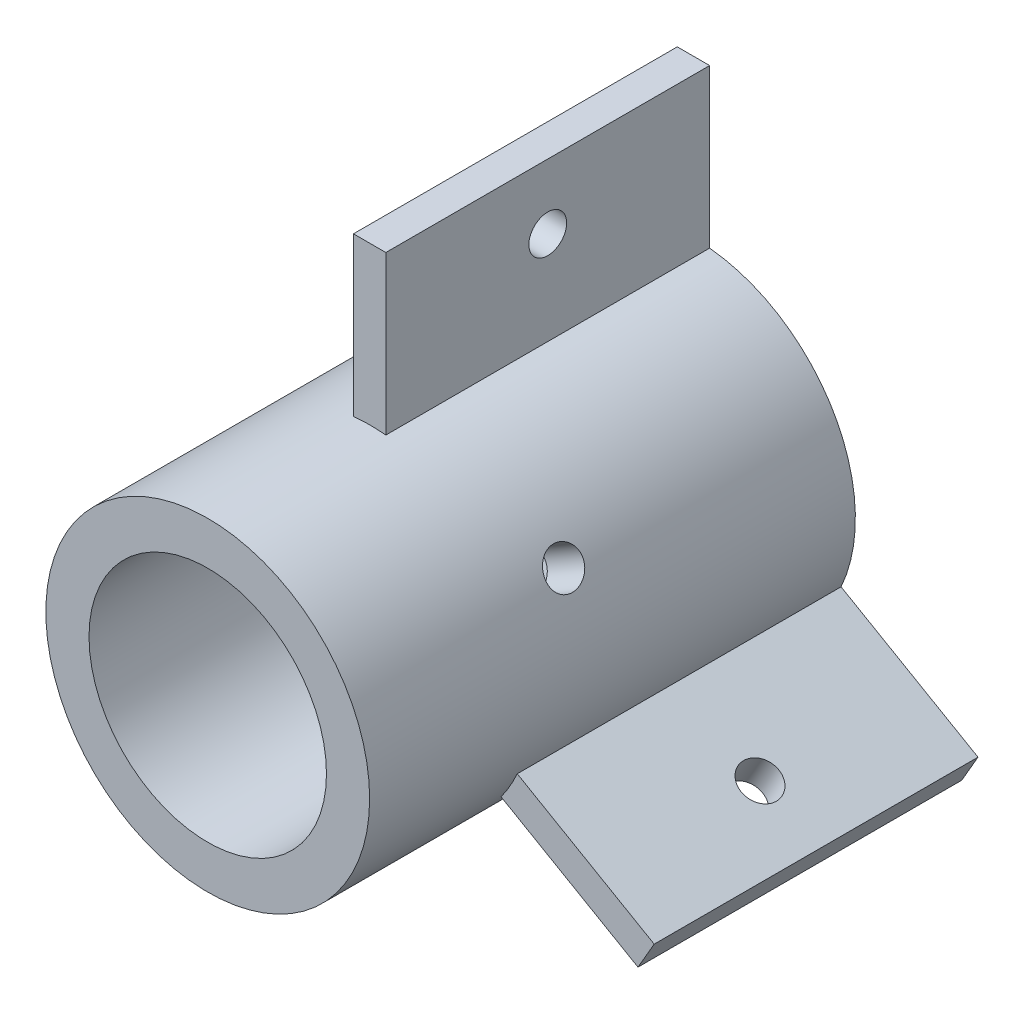
SolidWorks part; units mm, degrees
ref_plane "前基準面" through (0, 0, 0) normal (0, 0, 1) x (1, 0, 0)
ref_plane "上基準面" through (0, 0, 0) normal (0, 1, 0) x (1, 0, 0)
ref_plane "右基準面" through (0, 0, 0) normal (1, 0, 0) x (0, 0, -1)
sketch "草圖1" plane through (0, 0, 0) normal (0, 0, 1) x (1, 0, 0)
  circle A0 centre (0, 0) radius 15
  dimension "D1" = 30
extrude "填料-伸長1" add sketch "草圖1" along normal blind 45
sketch "草圖2" plane through (0, 0, 45) normal (0, 0, 1) x (1, 0, 0)
  circle A0 centre (0, 0) radius 11
  dimension "D1" = 22
extrude "除料-伸長1" cut sketch "草圖2" against normal blind 40
sketch "草圖3" plane through (0, 0, 5) normal (0, 0, 1) x (1, 0, 0)
  circle A0 centre (0, 0) radius 7.5
  dimension "D1" = 15
extrude "除料-伸長2" cut sketch "草圖3" against normal blind 5
sketch "草圖4" plane through (0, 0, 0) normal (0, 0, 1) x (1, 0, 0)
  line L0 (26.361, -13.4875) -> (13.3706, -5.9875)
  line L1 (-1.5, 29.5731) -> (1.5, 29.5731)
  line L2 (-1.5, 29.5731) -> (-1.5, 14.5731)
  line L3 (-1.5, 14.5731) -> (1.5, 14.5731)
  line L4 (1.5, 29.5731) -> (1.5, 14.5731)
  line L5 (26.361, -13.4875) -> (24.861, -16.0856)
  line L6 (24.861, -16.0856) -> (11.8706, -8.5856)
  line L7 (13.3706, -5.9875) -> (11.8706, -8.5856)
  line L8 (-24.861, -16.0856) -> (-11.8706, -8.5856)
  line L9 (-24.861, -16.0856) -> (-26.361, -13.4875)
  line L10 (-26.361, -13.4875) -> (-13.3706, -5.9875)
  line L11 (-11.8706, -8.5856) -> (-13.3706, -5.9875)
  point P4 (0, 14.5731)
  point P17 (0, 0)
  dimension "D1" = 15
  dimension "D2" = 3
  dimension "D3" = 14.5731
  dimension "D4" = 3
extrude "填料-伸長2" add sketch "草圖4" along normal blind 30
sketch "草圖5" plane through (-0.75, -1.299, 0) normal (-0.5, -0.866, 0) x (0.866, -0.5, 0)
  line L0 (29.5731, 30) -> (29.5731, 0) construction
  circle A0 centre (23.5731, 15) radius 1.75
  point P4 (29.5731, 15)
  dimension "D1" = 3.5
  dimension "D2" = 6
extrude "除料-伸長3" cut sketch "草圖5" against normal blind 30
sketch "草圖6" plane through (1.5, 0, 0) normal (1, 0, 0) x (0, 0, -1)
  line L0 (-30, 29.5731) -> (0, 29.5731) construction
  circle A0 centre (-15, 23.5731) radius 1.75
  point P6 (-15, 29.5731)
  dimension "D1" = 3.5
  dimension "D2" = 6
extrude "除料-伸長4" cut sketch "草圖6" against normal blind 30
sketch "草圖7" plane through (-0.75, 1.299, 0) normal (-0.5, 0.866, 0) x (0.866, 0.5, 0)
  line L0 (-29.5731, -30) -> (-29.5731, 0) construction
  circle A0 centre (-23.5731, -15) radius 1.75
  point P4 (-29.5731, -15)
  dimension "D1" = 3.5
  dimension "D2" = 6
extrude "除料-伸長5" cut sketch "草圖7" against normal blind 30
ref_plane "平面1" through (0, -15, 0) normal (0, -1, 0) x (0, 0, -1)
sketch "草圖8" plane through (0, -15, 0) normal (0, -1, 0) x (0, 0, -1)
  line L0 (24.75, 0) -> (-24.75, 0) construction
  line L1 (-36.0699, 0) -> (-37.8199, 0) construction
  line L2 (0, -12.1753) -> (0, 12.1753) construction
  circle A0 centre (-25, 0) radius 1.75
  dimension "D1" = 3.5
  dimension "D2" = 25
extrude "除料-伸長6" cut sketch "草圖8" against normal blind 10
pattern_circular "環狀複製排列1" count 3 every 120 about axis through (0, 0, 0) along (0, 0, 1) of "除料-伸長6"
